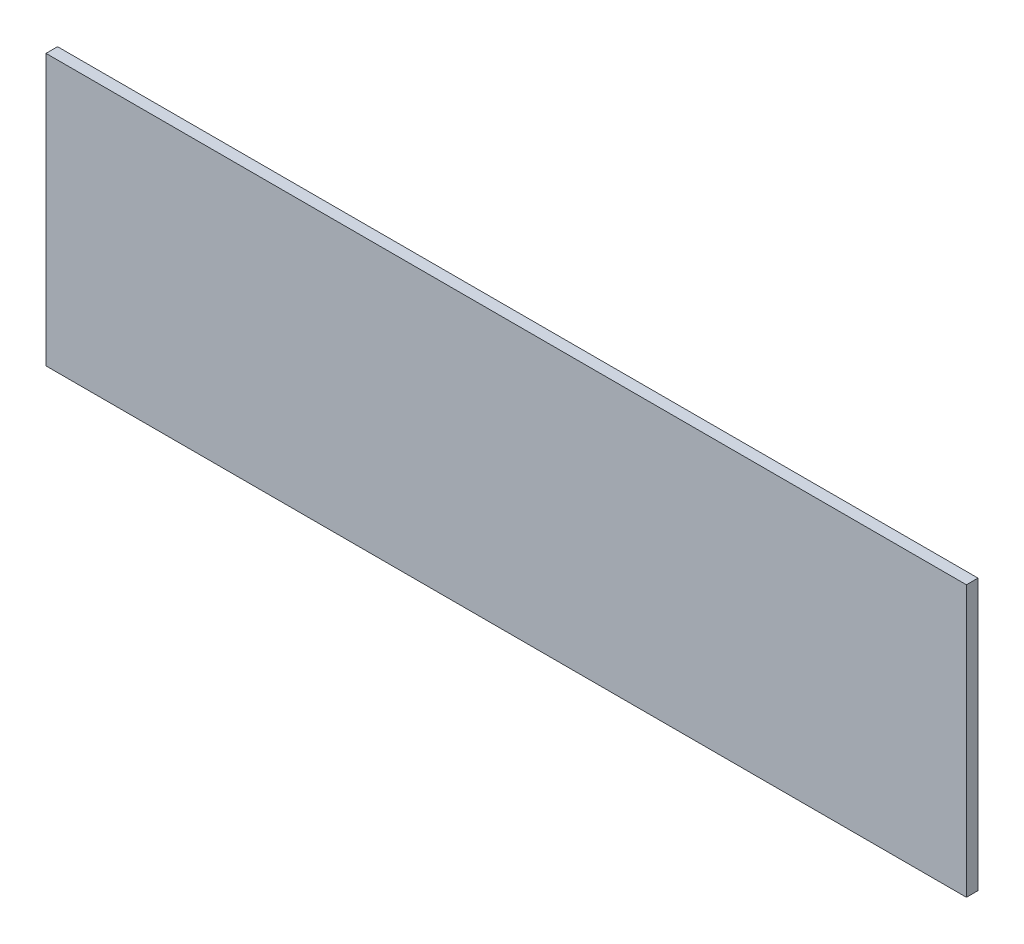
SolidWorks part; units mm, degrees
material "Pine"
ref_plane "Front Plane" through (0, 0, 0) normal (0, 0, 1) x (1, 0, 0)
ref_plane "Top Plane" through (0, 0, 0) normal (0, 1, 0) x (1, 0, 0)
ref_plane "Right Plane" through (0, 0, 0) normal (1, 0, 0) x (0, 0, -1)
sketch "Sketch1" plane through (0, 0, 0) normal (0, 0, 1) x (1, 0, 0)
  line L1 (473.3294, -408.6348) -> (-473.3294, -408.6348)
  line L2 (473.3294, -408.6348) -> (473.3294, -687.038)
  line L3 (473.3294, -687.038) -> (-473.3294, -687.038)
  line L4 (-473.3294, -408.6348) -> (-473.3294, -687.038)
extrude "Boss-Extrude1" add sketch "Sketch1" against normal up to surface (11.9063 mm away)
